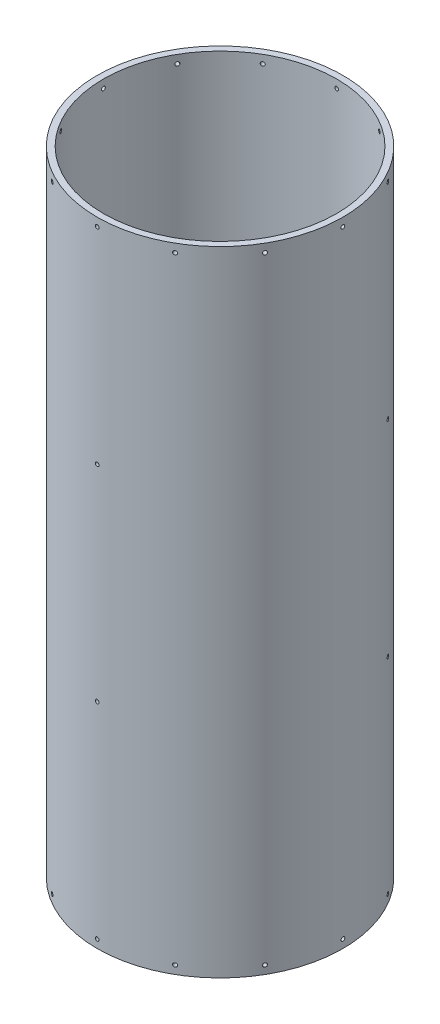
SolidWorks part; units mm, degrees
material "PVC Rigid"
ref_plane "Front Plane" through (0, 0, 0) normal (0, 0, 1) x (1, 0, 0)
ref_plane "Top Plane" through (0, 0, 0) normal (0, 1, 0) x (1, 0, 0)
ref_plane "Right Plane" through (0, 0, 0) normal (1, 0, 0) x (0, 0, -1)
sketch "Sketch1" plane through (0, 0, 0) normal (0, 1, 0) x (1, 0, 0)
  circle A0 centre (0, 0) radius 93.6625
  circle A1 centre (0, 0) radius 88.9
  dimension "D1" = 187.325
  dimension "D2" = 177.8
extrude "Boss-Extrude1" add sketch "Sketch1" along normal mid plane 482.854
ref_plane "Plane1" through (0, 0, 93.6625) normal (0, 0, 1) x (1, 0, 0)
sketch "Sketch3" plane through (0, 0, 93.6625) normal (0, 0, 1) x (1, 0, 0)
  line L0 (0, -55) -> (0, 55) construction
  line L1 (-93.6625, -241.427) -> (93.6625, -241.427) construction
  circle A0 centre (0, -235.077) radius 1.4351
  dimension "D1" = 2.8702
  dimension "D2" = 6.35
extrude "Cut-Extrude1" cut sketch "Sketch3" against normal blind 19.304
pattern_circular "CirPattern1" count 12 over 360 about axis through (0, 241.427, 0) along (0, -1, 0) of "Cut-Extrude1"
mirror "Mirror1" about plane through (0, 0, 0) normal (0, 1, 0) of "CirPattern1", "Cut-Extrude1"
sketch "Sketch4" plane through (0, 0, 93.6625) normal (0, 0, 1) x (1, 0, 0)
  line L0 (0, -103.0288) -> (0, 103.0288) construction
  circle A0 centre (0, -78.359) radius 1.4351
  circle A1 centre (0, 78.359) radius 1.4351
  circle A2 centre (0, 235.077) radius 1.4351 construction
  circle A3 centre (0, -235.077) radius 1.4351 construction
  dimension "D1" = 2.8702
  dimension "D2" = 2.8702
  dimension "D3" = 156.718
  dimension "D4" = 156.718
extrude "Cut-Extrude2" cut sketch "Sketch4" against normal blind 25.146
pattern_circular "CirPattern2" count 3 over 360 about axis through (0, 241.427, 0) along (0, -1, 0) of "Cut-Extrude2"
